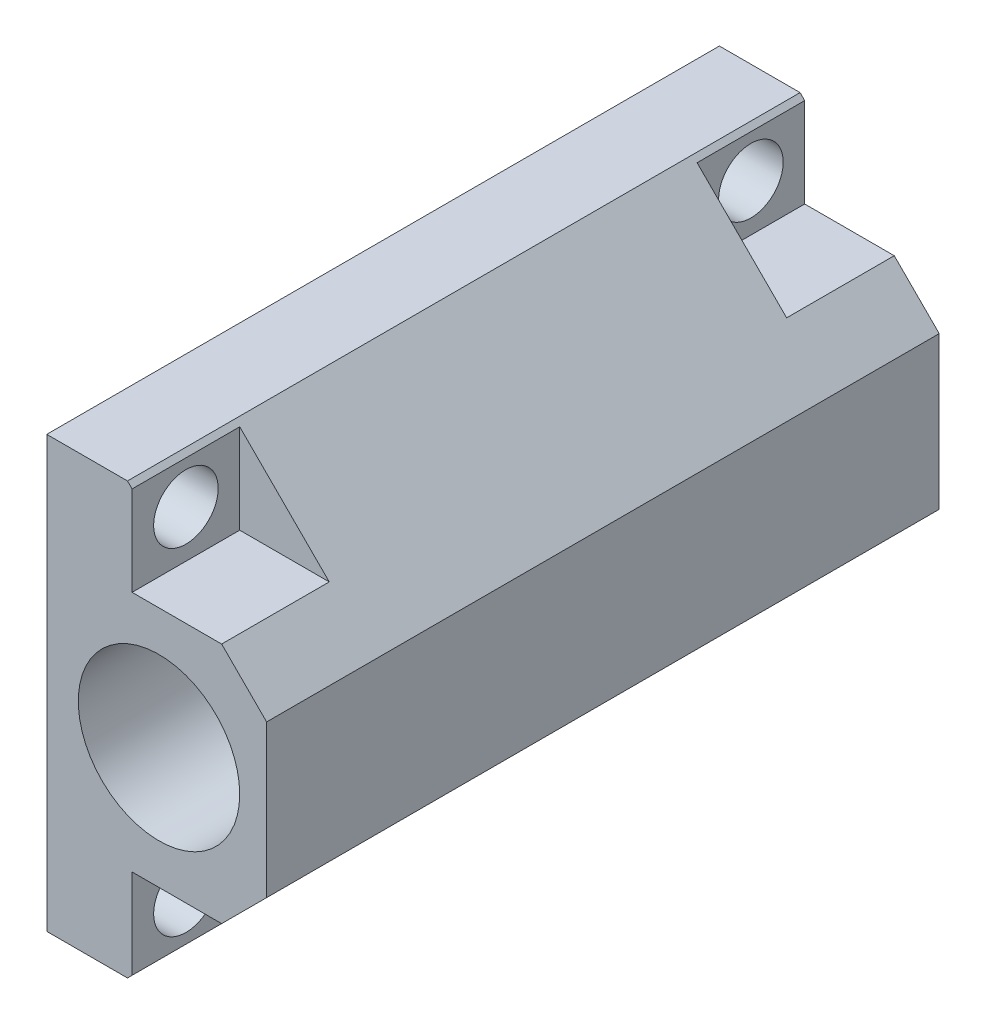
SolidWorks part; units mm, degrees
ref_plane "Front Plane" through (0, 0, 0) normal (0, 0, 1) x (1, 0, 0)
ref_plane "Top Plane" through (0, 0, 0) normal (0, 1, 0) x (1, 0, 0)
ref_plane "Right Plane" through (0, 0, 0) normal (1, 0, 0) x (0, 0, -1)
sketch "Sketch1" plane through (0, 0, 0) normal (0, 0, 1) x (1, 0, 0)
  line L1 (-1.5, -8) -> (1.5, -8)
  line L2 (-1.5, -8) -> (-1.5, 8)
  line L3 (-1.5, 8) -> (1.5, 8)
  line L4 (1.5, -8) -> (1.5, 8)
  line L5 (-1.5, -8) -> (1.5, 8) construction
  line L6 (-1.5, 8) -> (1.5, -8) construction
  point P0 (0, 0)
  dimension "D1" = 3
  dimension "D2" = 16
extrude "Boss-Extrude1" add sketch "Sketch1" along normal blind 25
sketch "Sketch4" plane through (0, 0, 25) normal (0, 0, 1) x (1, 0, 0)
  line L0 (1.5, 8) -> (9.5, 0)
  line L1 (9.5, 0) -> (1.5, -8)
  line L2 (1.5, 8) -> (1.5, -8)
extrude "Boss-Extrude2" add sketch "Sketch4" against normal through all
hole_wizard "M2 Clearance Hole1" positions "Sketch2" profile "Sketch3" hole size "M2" standard "ANSI Metric"
sketch "Sketch2" plane through (-1.5, 0, 0) normal (1, 0, 0) x (0, 0, -1)
  line L1 (-23, -6.25) -> (-2, -6.25)
  line L2 (-23, -6.25) -> (-23, 6.25)
  line L3 (-23, 6.25) -> (-2, 6.25)
  line L4 (-2, -6.25) -> (-2, 6.25)
  line L5 (-23, -6.25) -> (-2, 6.25) construction
  line L6 (-23, 6.25) -> (-2, -6.25) construction
  point P1 (-2, 6.25)
  point P60 (-23, -6.25)
  point P61 (-23, 6.25)
  point P62 (-2, -6.25)
  dimension "D1" = 12.5
  dimension "D2" = 21
sketch "Sketch3" plane through (-1.5, 6.25, 2) normal (0, 1, 0) x (0, 0, 1)
  line L0 (0, 0) -> (0, 4.75)
  line L1 (0, 4.75) -> (1.2, 4.75)
  line L2 (1.2, 4.75) -> (1.2, 0)
  line L5 (1.2, 0) -> (0, 0)
  line L11 (0, -6.35) -> (0, 107.95) construction
  dimension "Thru Hole Dia." = 2.4
  dimension "Thru Hole Depth" = 4.75
chamfer "Chamfer1" distance 4 angle 45 1 edges at (9.5, 0, 12.5)
hole_wizard "Ø6.0mm Dowel Hole3" positions "Sketch6" profile "Sketch8" hole size "Ø6.0" standard "ANSI Metric"
sketch "Sketch6" plane through (0, 0, 25) normal (0, 0, 1) x (1, 0, 0)
  line L0 (6.6716, -2.8284) -> (6.6716, 2.8284) construction
  point P0 (2.6716, 0)
  dimension "D1" = 4
sketch "Sketch8" plane through (2.6716, 0, 25) normal (1, 0, 0) x (0, -1, 0)
  line L0 (0, 0) -> (0, 9.8026)
  line L1 (0, 9.8026) -> (3, 8)
  line L2 (3, 8) -> (3, 0)
  line L5 (3, 0) -> (0, 0)
  line L10 (0, 9.8026) -> (-3, 8) construction
  line L11 (0, -6.35) -> (0, 107.95) construction
  dimension "Hole Dia." = 6
  dimension "Hole Depth" = 8
  dimension "Drill Angle" = 118
ref_plane "Plane1" through (0, 0, 12.5) normal (0, 0, 1) x (1, 0, 0)
mirror "Mirror2" about plane through (0, 0, 12.5) normal (0, 0, 1) of "Ø6.0mm Dowel Hole3"
sketch "Sketch12" plane through (6.6716, 0, 0) normal (1, 0, 0) x (0, 0, -1)
  line L1 (-4, 4.5) -> (0, 4.5)
  line L2 (-4, 4.5) -> (-4, 8)
  line L3 (-4, 8) -> (0, 8)
  line L4 (0, -8) -> (0, 8)
  line L5 (-25, -8) -> (0, -8)
  line L6 (-25, 8) -> (-25, -8)
  line L7 (0, 8) -> (-25, 8)
  line L8 (0, -8) -> (0, 8)
  line L9 (-25, -8) -> (0, -8)
  line L10 (-25, 8) -> (-25, -8)
  line L11 (0, 8) -> (-25, 8)
  line L12 (0, 4.5) -> (0, 8)
  line L13 (-4, 4.5) -> (0, 8) construction
  line L14 (-4, 8) -> (0, 4.5) construction
  line L15 (-4, -4.5) -> (0, -4.5)
  line L16 (-4, -4.5) -> (-4, -8)
  line L17 (-4, -8) -> (0, -8)
  line L18 (0, -4.5) -> (0, -8)
  line L19 (-4, -4.5) -> (0, -8) construction
  line L20 (-4, -8) -> (0, -4.5) construction
  line L21 (-21, -4.5) -> (-25, -4.5)
  line L22 (-21, -4.5) -> (-21, -8)
  line L23 (-21, -8) -> (-25, -8)
  line L24 (-25, -4.5) -> (-25, -8)
  line L25 (-21, -4.5) -> (-25, -8) construction
  line L26 (-21, -8) -> (-25, -4.5) construction
  line L27 (-21, 4.5) -> (-25, 4.5)
  line L28 (-21, 4.5) -> (-21, 8)
  line L29 (-21, 8) -> (-25, 8)
  line L30 (-25, 4.5) -> (-25, 8)
  line L31 (-21, 4.5) -> (-25, 8) construction
  line L32 (-21, 8) -> (-25, 4.5) construction
  circle A0 centre (-23, 6.25) radius 1.2 construction
  circle A1 centre (-23, -6.25) radius 1.2 construction
  circle A2 centre (-2, -6.25) radius 1.2 construction
  circle A3 centre (-2, 6.25) radius 1.2 construction
  circle A4 centre (-23, 6.25) radius 1.2
  circle A5 centre (-23, -6.25) radius 1.2
  circle A6 centre (-2, -6.25) radius 1.2
  circle A7 centre (-2, 6.25) radius 1.2
  dimension "D1" = 0
extrude "Cut-Extrude1" cut sketch "Sketch12" against normal blind 5 contours L1 L8 L3 L2 A7 | A7 | A6 | L15 L16 L9 L8 A6 | A5 | L22 L21 L10 L9 A5 | A4 | L27 L28 L11 L10 A4
